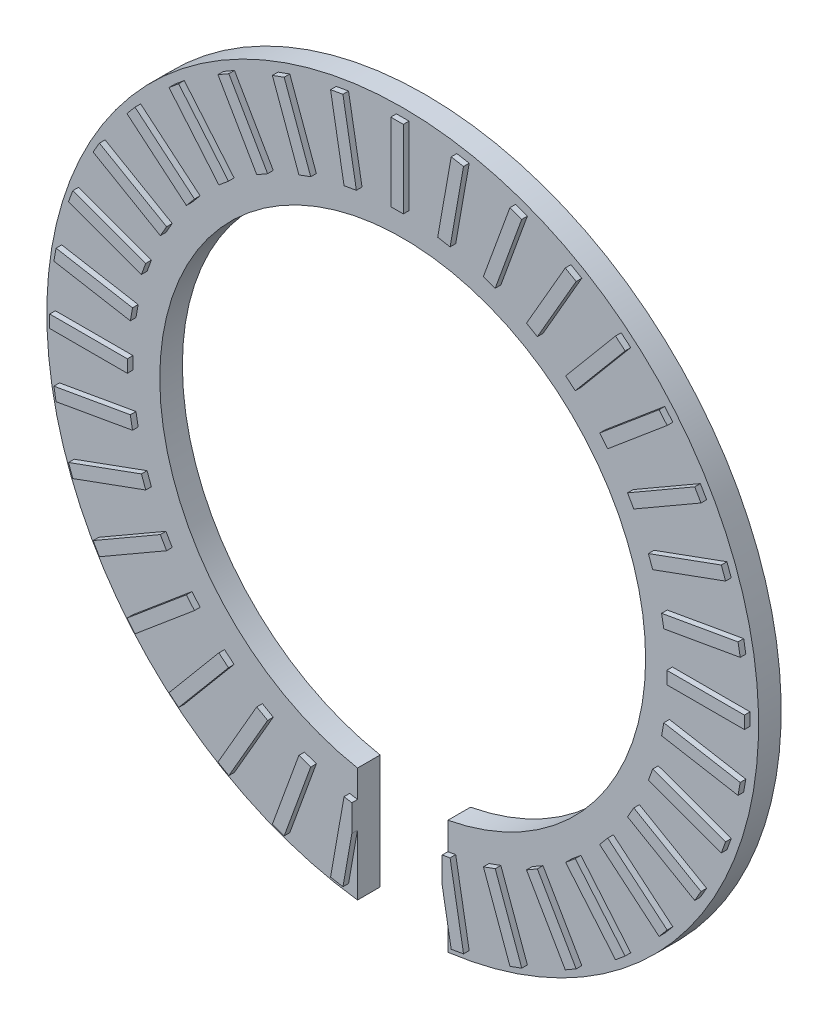
SolidWorks part; units mm, degrees
ref_plane "Plan de face" through (0, 0, 0) normal (0, 0, 1) x (1, 0, 0)
ref_plane "Plan de dessus" through (0, 0, 0) normal (0, 1, 0) x (1, 0, 0)
ref_plane "Plan de droite" through (0, 0, 0) normal (1, 0, 0) x (0, 0, -1)
sketch "Esquisse1" plane through (0, 0, 0) normal (0, 0, 1) x (1, 0, 0)
  circle A0 centre (0, 0) radius 21.5
  circle A1 centre (0, 0) radius 31.5
  dimension "D1" = 43
  dimension "D2" = 10
extrude "Boss.-Extru.1" add sketch "Esquisse1" along normal blind 2 contours A1 | A0
sketch "Esquisse2" plane through (0, 0, 2) normal (0, 0, 1) x (1, 0, 0)
  line L1 (0.5552, 30.7407) -> (-0.5552, 30.7407)
  line L2 (0.5552, 30.7407) -> (0.5552, 23.8733)
  line L3 (0.5552, 23.8733) -> (-0.5552, 23.8733)
  line L4 (-0.5552, 30.7407) -> (-0.5552, 23.8733)
  line L5 (0.5552, 30.7407) -> (-0.5552, 23.8733) construction
  line L6 (0.5552, 23.8733) -> (-0.5552, 30.7407) construction
  point P0 (0, 27.307)
  dimension "D1" = 1.1103
extrude "Boss.-Extru.2" add sketch "Esquisse2" along normal blind 0.5
pattern_circular "Répétition circulaire1" count 36 every 10 about axis through (0, 0, 0) along (0, 0, 1) of "Boss.-Extru.2"
sketch "Esquisse3" plane through (0, 0, 2) normal (0, 0, 1) x (1, 0, 0)
  line L9 (0, 0) -> (-4, 0)
  line L11 (0, -36.5234) -> (-4, -36.5234)
  line L12 (-4, 0) -> (-4, -36.5234)
  line L13 (0, 0) -> (4, 0)
  line L15 (0, -36.5234) -> (4, -36.5234)
  line L16 (4, 0) -> (4, -36.5234)
  dimension "D1" = 4
  dimension "D2" = 4
extrude "Enlèv. mat.-Extru.4" cut sketch "Esquisse3" against normal through all both and the other way through all contours L16 L15 L11 L12 L9 L13
